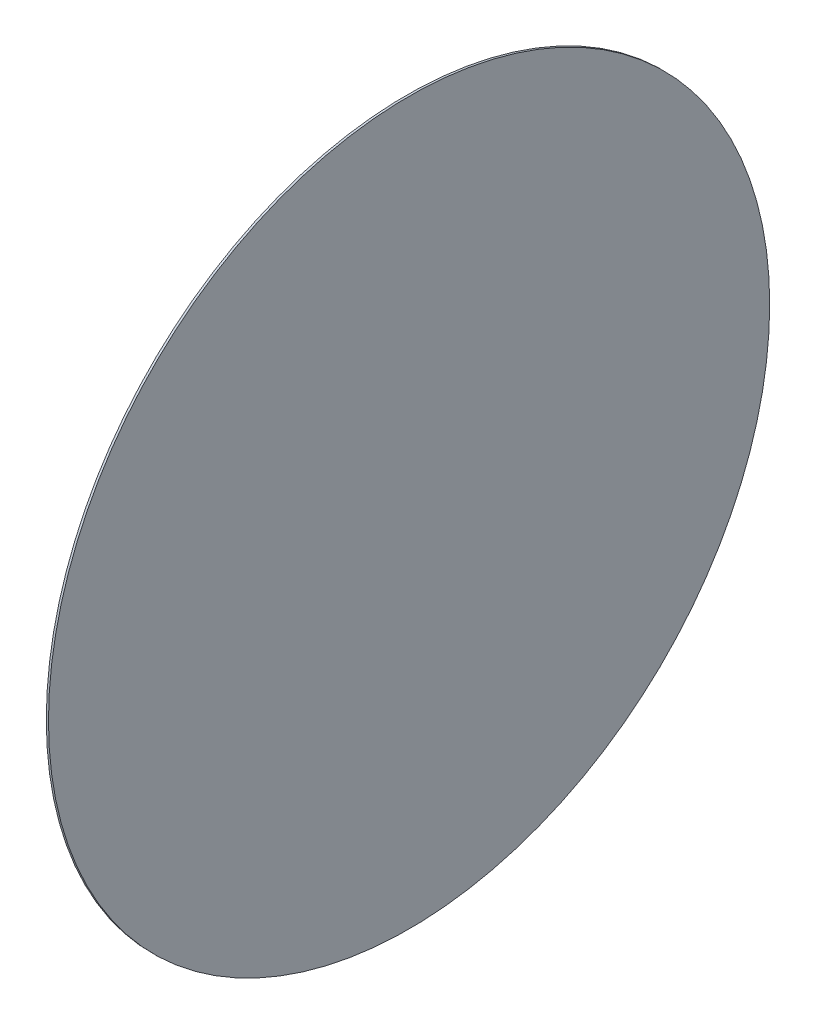
SolidWorks part; units mm, degrees
ref_plane "前视基准面" through (0, 0, 0) normal (0, 0, 1) x (1, 0, 0)
ref_plane "上视基准面" through (0, 0, 0) normal (0, 1, 0) x (1, 0, 0)
ref_plane "右视基准面" through (0, 0, 0) normal (1, 0, 0) x (0, 0, -1)
sketch "草图1" plane through (0, 0, 0) normal (0, 0, 1) x (1, 0, 0)
  line L0 (0, 9) -> (0, 0)
  line L2 (0, 9) -> (0.054, 9)
  line L3 (0, 0) -> (0.054, 0)
  line L4 (0.054, 9) -> (0.054, 0)
  dimension "D1" = 9
  dimension "D2" = 0.054
revolve "旋转2" add sketch "草图1" angle 360 about L3
